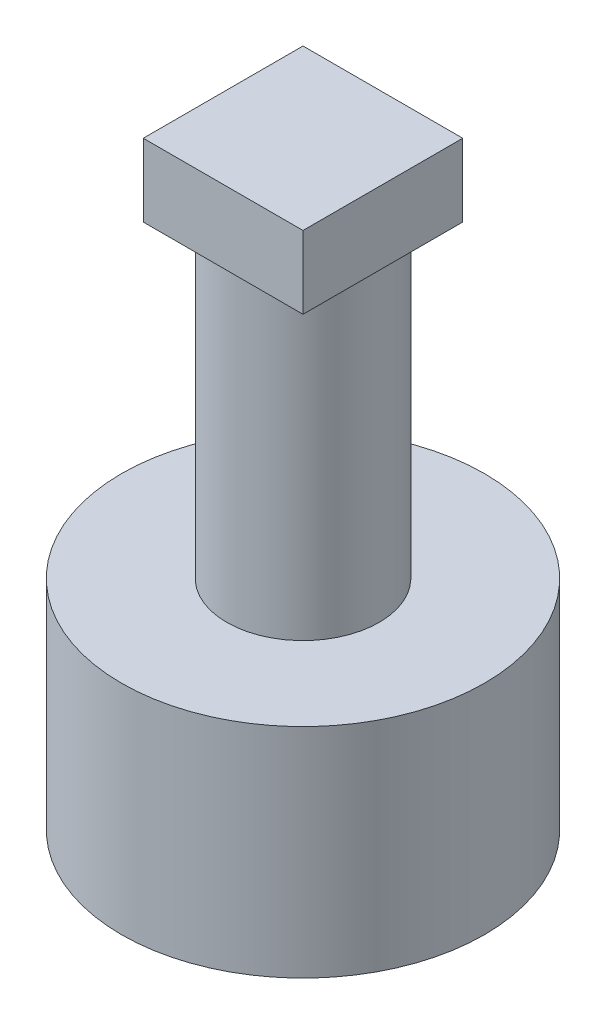
SolidWorks part; units mm, degrees
ref_plane "Front Plane" through (0, 0, 0) normal (0, 0, 1) x (1, 0, 0)
ref_plane "Top Plane" through (0, 0, 0) normal (0, 1, 0) x (1, 0, 0)
ref_plane "Right Plane" through (0, 0, 0) normal (1, 0, 0) x (0, 0, -1)
sketch "Sketch1" plane through (0, 0, 0) normal (0, 1, 0) x (1, 0, 0)
  line L1 (-3.3, 2.55) -> (3.3, 2.55)
  line L2 (-3.3, 2.55) -> (-3.3, -2.55)
  line L3 (-3.3, -2.55) -> (3.3, -2.55)
  line L4 (3.3, 2.55) -> (3.3, -2.55)
  line L5 (-3.3, 2.55) -> (3.3, -2.55) construction
  line L6 (-3.3, -2.55) -> (3.3, 2.55) construction
  circle A1 centre (0, 0) radius 5
  dimension "D2" = 10
  dimension "D1" = 5.1
  dimension "D3" = 6.6
extrude "Boss-Extrude1" add sketch "Sketch1" along normal blind 5
sketch "Sketch2" plane through (0, 5, 0) normal (0, 1, 0) x (1, 0, 0)
  circle A0 centre (0, 0) radius 5
  dimension "D1" = 10
extrude "Boss-Extrude2" add sketch "Sketch2" along normal blind 1
sketch "Sketch3" plane through (0, 6, 0) normal (0, 1, 0) x (1, 0, 0)
  circle A0 centre (0, 0) radius 2.1
  dimension "D1" = 4.2
extrude "Boss-Extrude3" add sketch "Sketch3" along normal blind 8.5
sketch "Sketch4" plane through (0, 14.5, 0) normal (0, 1, 0) x (1, 0, 0)
  line L1 (-2.2, -2.2) -> (2.2, -2.2)
  line L2 (-2.2, -2.2) -> (-2.2, 2.2)
  line L3 (-2.2, 2.2) -> (2.2, 2.2)
  line L4 (2.2, -2.2) -> (2.2, 2.2)
  line L5 (-2.2, -2.2) -> (2.2, 2.2) construction
  line L6 (-2.2, 2.2) -> (2.2, -2.2) construction
  point P0 (0, 0)
  dimension "D1" = 4.4
extrude "Boss-Extrude4" add sketch "Sketch4" along normal blind 2
